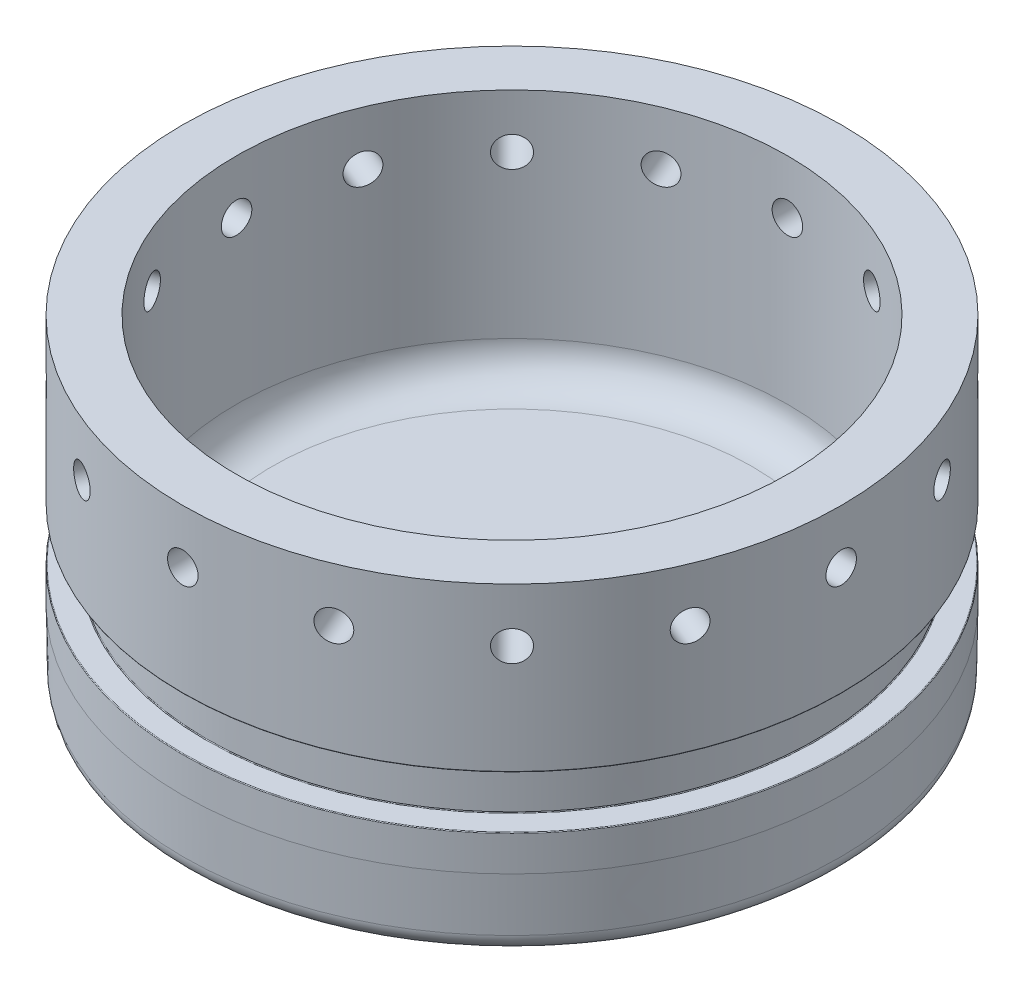
SolidWorks part; units mm, degrees
material "6061-T6 (SS)"
ref_plane "Front Plane" through (0, 0, 0) normal (0, 0, 1) x (1, 0, 0)
ref_plane "Top Plane" through (0, 0, 0) normal (0, 1, 0) x (1, 0, 0)
ref_plane "Right Plane" through (0, 0, 0) normal (1, 0, 0) x (0, 0, -1)
sketch "Sketch1" plane through (0, 0, 0) normal (0, 0, 1) x (1, 0, 0)
  line L1 (0, -9.525) -> (58.4454, -9.525)
  line L2 (58.4454, -9.525) -> (58.4454, 41.275) construction
  line L3 (0, 47.7012) -> (9.525, 47.7012)
  line L4 (58.4454, -9.525) -> (58.4454, 3.175)
  line L5 (58.4454, 3.175) -> (9.525, 3.175)
  line L6 (9.525, 3.175) -> (9.525, 47.7012)
  line L8 (0, -9.525) -> (0, 9.525)
  line L20 (0, 9.525) -> (4.318, 9.525)
  line L21 (4.318, 9.525) -> (4.318, 18.796)
  line L22 (4.318, 18.796) -> (0, 18.796)
  line L23 (0, 47.7012) -> (0, 18.796)
  line L24 (0, 3.175) -> (0.2217, -9.525)
  dimension "D2" = 58.4454
  dimension "D3" = 12.7
  dimension "D4" = 19.05
  dimension "D5" = 4.318
  dimension "D6" = 18.796
  dimension "D7" = 3.175
  dimension "D8" = 47.7012
  dimension "D9" = 0.2217
  dimension "D11" = 9.525
revolve "Revolve1" add sketch "Sketch1" angle 360 about L2
ref_plane "HoleReferencePlane" through (0, 0, 58.4454) normal (0, 0, 1) x (1, 0, 0)
sketch "Centerline" plane through (0, 0, 0) normal (0, 0, 1) x (1, 0, 0)
  line L0 (58.4454, 47.7012) -> (58.4454, -9.525) construction
  line L2 (0, -9.525) -> (116.8908, -9.525) construction
fillet "PocketFillet" radius 6.35 1 edges at (58.4454, 3.175, -48.9204)
fillet "TaperFillet" radius 3.175 1 edges at (58.4454, -9.525, -58.2237)
sketch "Sketch7" plane through (0, 0, 0) normal (0, 1, 0) x (1, 0, 0)
  line L0 (116.8908, 0) -> (58.4454, 0)
  line L1 (58.4454, 0) -> (83.8454, 0)
  circle A0 centre (58.4454, 0) radius 58.4454 construction
  point P11 (83.8454, 0)
hole_wizard "Pipe Tap Drill for 1/8 Tap1" positions "Sketch8" profile "Sketch9" hole size "1/8" standard "ANSI Inch" end condition through all
sketch "Sketch8" plane through (0, 3.175, 0) normal (0, 1, 0) x (1, 0, 0)
  point P3 (83.8454, 0)
  point P10 (0, 0)
sketch "Sketch9" plane through (83.8454, 3.175, 0) normal (1, 0, 0) x (0, 0, 1)
  line L0 (0, 0) -> (0, 12.7)
  line L1 (0, 12.7) -> (4.2164, 12.7)
  line L2 (4.2164, 12.7) -> (4.2164, 0)
  line L5 (4.2164, 0) -> (0, 0)
  line L11 (0, -6.35) -> (0, 107.95) construction
  dimension "Thru Hole Dia." = 8.4328
  dimension "Thru Hole Depth" = 12.7
hole_wizard "Pipe Tap Drill for 1/4 Tap1" positions "Sketch13" profile "Sketch14" hole size "1/4" standard "ANSI Inch"
sketch "Sketch13" plane through (0, 3.175, 0) normal (0, 1, 0) x (1, 0, 0)
  point P0 (33.3375, 0)
sketch "Sketch14" plane through (33.3375, 3.175, 0) normal (1, 0, 0) x (0, 0, 1)
  line L0 (0, 0) -> (0, 12.7)
  line L1 (0, 12.7) -> (5.5626, 12.7)
  line L2 (5.5626, 12.7) -> (5.5626, 0)
  line L5 (5.5626, 0) -> (0, 0)
  line L11 (0, -6.35) -> (0, 107.95) construction
  dimension "Thru Hole Dia." = 11.1252
  dimension "Thru Hole Depth" = 12.7
fillet "Fillet3" radius 0.127 4 edges at (58.4454, 9.525, -58.4454) (58.4454, 9.525, -54.1274) (58.4454, 18.796, -54.1274) (58.4454, 18.796, -58.4454)
sketch "HoleReferencePoint" plane through (0, 0, 58.4454) normal (0, 0, 1) x (1, 0, 0)
  line L0 (116.8908, 47.7012) -> (0, 47.7012) construction
  point P0 (58.4454, 38.1762)
  dimension "D1" = 9.525
  dimension "D2" = 58.4454
hole_wizard "Tap Drill for 1/4-28 Tap1" positions "Sketch17" profile "Sketch16" hole size "1/4-28" standard "ANSI Inch" end condition through all
sketch "Sketch17" plane through (0, 0, 58.4454) normal (0, 0, 1) x (1, 0, 0)
  point P0 (58.4454, 38.1762)
sketch "Sketch16" plane through (58.4454, 38.1762, 58.4454) normal (1, 0, 0) x (0, -1, 0)
  line L0 (0, 0) -> (0, 116.8908)
  line L1 (0, 116.8908) -> (2.7051, 116.8908)
  line L2 (2.7051, 116.8908) -> (2.7051, 0)
  line L5 (2.7051, 0) -> (0, 0)
  line L11 (0, -6.35) -> (0, 107.95) construction
  dimension "Thru Hole Dia." = 5.4102
  dimension "Thru Hole Depth" = 116.8908
pattern_circular "HolePattern" count 16 over 360 about axis through (58.4454, 47.7012, 0) along (0, -1, 0) of "Tap Drill for 1/4-28 Tap1"
